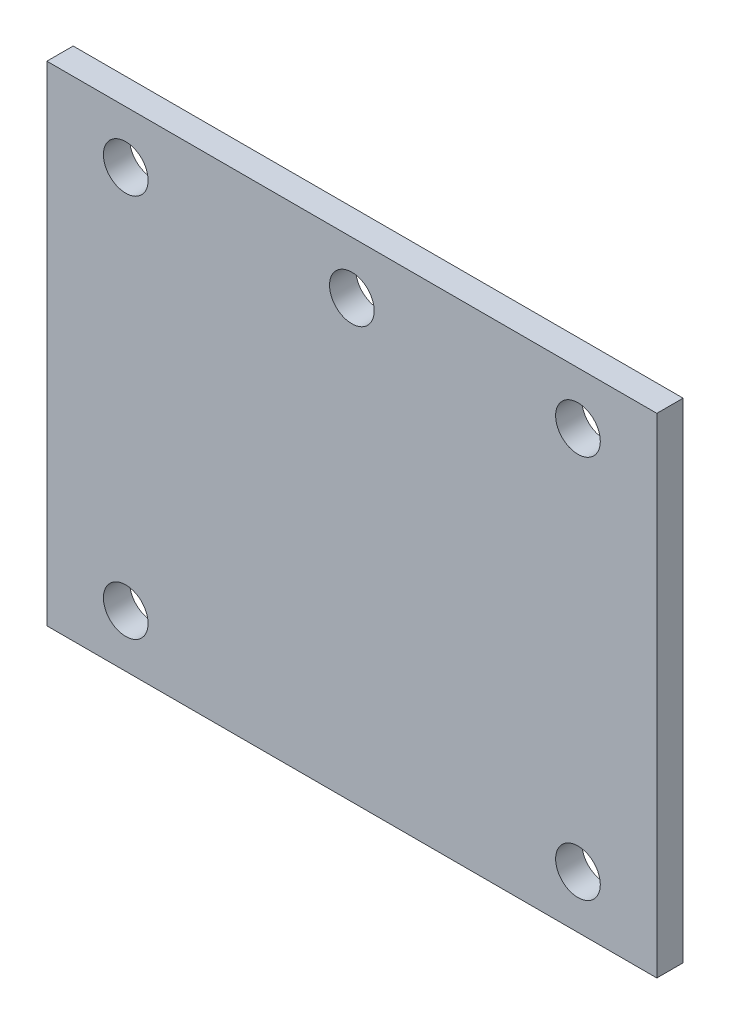
SolidWorks part; units mm, degrees
material "1.0116 (S235J2G3)"
ref_plane "Front Plane" through (0, 0, 0) normal (0, 0, 1) x (1, 0, 0)
ref_plane "Top Plane" through (0, 0, 0) normal (0, 1, 0) x (1, 0, 0)
ref_plane "Right Plane" through (0, 0, 0) normal (1, 0, 0) x (0, 0, -1)
sketch "Sketch1" plane through (0, 0, 0) normal (0, 0, 1) x (1, 0, 0)
  line L1 (-58, -46.5) -> (58, -46.5)
  line L2 (-58, -46.5) -> (-58, 46.5)
  line L3 (-58, 46.5) -> (58, 46.5)
  line L4 (58, -46.5) -> (58, 46.5)
  line L5 (-58, -46.5) -> (58, 46.5) construction
  line L6 (-58, 46.5) -> (58, -46.5) construction
  circle A0 centre (-43, 36.5) radius 4.25
  circle A1 centre (43, 36.5) radius 4.25
  circle A2 centre (43, -36.5) radius 4.25
  circle A3 centre (-43, -36.5) radius 4.25
  circle A4 centre (0, 36.5) radius 4.25
  point P0 (0, 0)
  dimension "D3" = 8.5
  dimension "D4" = 10
  dimension "D5" = 15
  dimension "D9" = 43
  dimension "D10" = 43
  dimension "D11" = 73
  dimension "D12" = 15
  dimension "D1" = 93
  dimension "D2" = 116
  dimension "D7" = 2
  dimension "D6" = 2
  dimension "D8" = 2
extrude "Boss-Extrude1" add sketch "Sketch1" along normal blind 5
